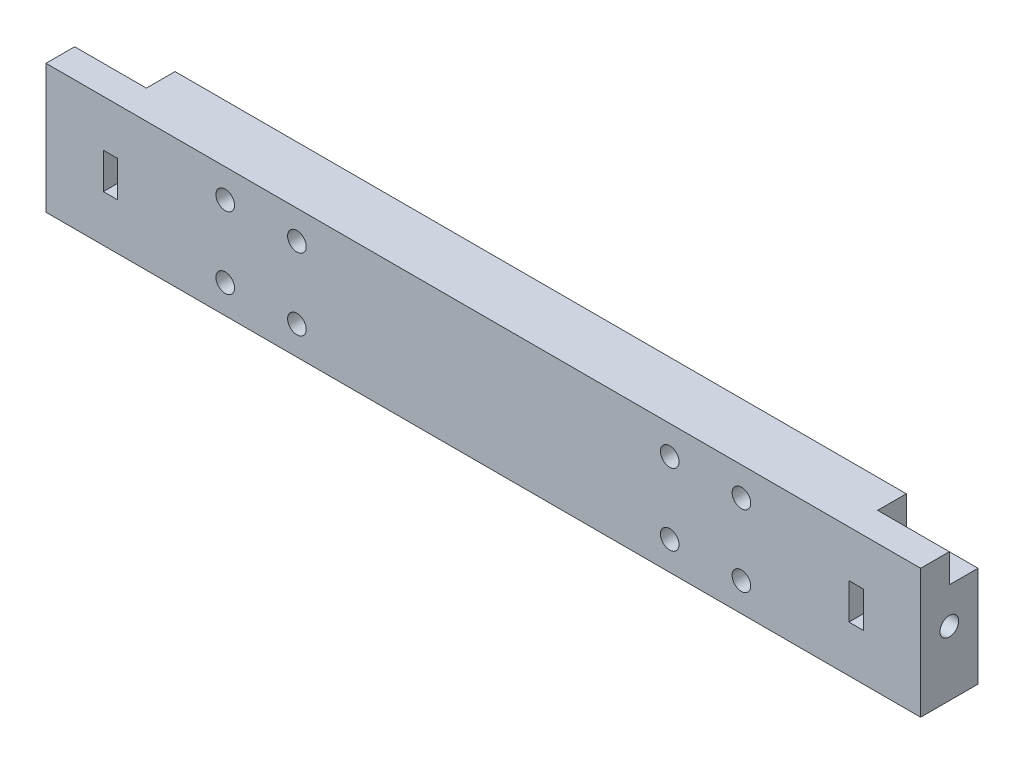
SolidWorks part; units mm, degrees
ref_plane "Front Plane" through (0, 0, 0) normal (0, 0, 1) x (1, 0, 0)
ref_plane "Top Plane" through (0, 0, 0) normal (0, 1, 0) x (1, 0, 0)
ref_plane "Right Plane" through (0, 0, 0) normal (1, 0, 0) x (0, 0, -1)
sketch "Sketch1" plane through (0, 0, 0) normal (0, 0, 1) x (1, 0, 0)
  line L1 (-61, 9) -> (61, 9)
  line L2 (-61, 9) -> (-61, -9)
  line L3 (-61, -9) -> (61, -9)
  line L4 (61, 9) -> (61, -9)
  line L5 (-61, 9) -> (61, -9) construction
  line L6 (-61, -9) -> (61, 9) construction
  line L7 (-36, 5) -> (36, 5) construction
  line L8 (-36, 5) -> (-36, -5) construction
  line L9 (-36, -5) -> (36, -5) construction
  line L10 (36, 5) -> (36, -5) construction
  line L11 (-36, 5) -> (36, -5) construction
  line L12 (-36, -5) -> (36, 5) construction
  line L13 (-26, 5) -> (26, 5) construction
  line L14 (-26, 5) -> (-26, -5) construction
  line L15 (-26, -5) -> (26, -5) construction
  line L16 (26, 5) -> (26, -5) construction
  line L17 (-26, 5) -> (26, -5) construction
  line L18 (-26, -5) -> (26, 5) construction
  circle A0 centre (-26, 5) radius 1.3
  circle A1 centre (-36, 5) radius 1.3
  circle A2 centre (-26, -5) radius 1.3
  circle A3 centre (-36, -5) radius 1.3
  circle A4 centre (26, -5) radius 1.3
  circle A5 centre (36, -5) radius 1.3
  circle A6 centre (36, 5) radius 1.3
  circle A7 centre (26, 5) radius 1.3
  point P0 (0, 0)
  point P6 (0, 0)
  point P11 (0, 0)
  dimension "D6" = 2.6
  dimension "D1" = 122
  dimension "D2" = 18
  dimension "D3" = 10
  dimension "D4" = 52
  dimension "D5" = 10
extrude "Boss-Extrude1" add sketch "Sketch1" along normal blind 8
sketch "Sketch2" plane through (0, 0, 0) normal (0, 0, -1) x (-1, 0, 0)
  line L1 (-36, 2) -> (-33.4019, 3.5)
  line L2 (-33.4019, 3.5) -> (-33.4019, 6.5)
  line L3 (-33.4019, 6.5) -> (-36, 8)
  line L4 (-36, 8) -> (-38.5981, 6.5)
  line L5 (-38.5981, 6.5) -> (-38.5981, 3.5)
  line L6 (-38.5981, 3.5) -> (-36, 2)
  line L7 (-26, 2) -> (-23.4019, 3.5)
  line L8 (-23.4019, 3.5) -> (-23.4019, 6.5)
  line L9 (-23.4019, 6.5) -> (-26, 8)
  line L10 (-26, 8) -> (-28.5981, 6.5)
  line L11 (-28.5981, 6.5) -> (-28.5981, 3.5)
  line L12 (-28.5981, 3.5) -> (-26, 2)
  line L13 (-26, -8) -> (-23.4019, -6.5)
  line L14 (-23.4019, -6.5) -> (-23.4019, -3.5)
  line L15 (-23.4019, -3.5) -> (-26, -2)
  line L16 (-26, -2) -> (-28.5981, -3.5)
  line L17 (-28.5981, -3.5) -> (-28.5981, -6.5)
  line L18 (-28.5981, -6.5) -> (-26, -8)
  line L19 (-36, -8) -> (-33.4019, -6.5)
  line L20 (-33.4019, -6.5) -> (-33.4019, -3.5)
  line L21 (-33.4019, -3.5) -> (-36, -2)
  line L22 (-36, -2) -> (-38.5981, -3.5)
  line L23 (-38.5981, -3.5) -> (-38.5981, -6.5)
  line L24 (-38.5981, -6.5) -> (-36, -8)
  line L25 (26, 2) -> (28.5981, 3.5)
  line L26 (28.5981, 3.5) -> (28.5981, 6.5)
  line L27 (28.5981, 6.5) -> (26, 8)
  line L28 (26, 8) -> (23.4019, 6.5)
  line L29 (23.4019, 6.5) -> (23.4019, 3.5)
  line L30 (23.4019, 3.5) -> (26, 2)
  line L31 (26, -8) -> (28.5981, -6.5)
  line L32 (28.5981, -6.5) -> (28.5981, -3.5)
  line L33 (28.5981, -3.5) -> (26, -2)
  line L34 (26, -2) -> (23.4019, -3.5)
  line L35 (23.4019, -3.5) -> (23.4019, -6.5)
  line L36 (23.4019, -6.5) -> (26, -8)
  line L37 (36, -8) -> (38.5981, -6.5)
  line L38 (38.5981, -6.5) -> (38.5981, -3.5)
  line L39 (38.5981, -3.5) -> (36, -2)
  line L40 (36, -2) -> (33.4019, -3.5)
  line L41 (33.4019, -3.5) -> (33.4019, -6.5)
  line L42 (33.4019, -6.5) -> (36, -8)
  line L43 (36, 2) -> (38.5981, 3.5)
  line L44 (38.5981, 3.5) -> (38.5981, 6.5)
  line L45 (38.5981, 6.5) -> (36, 8)
  line L46 (36, 8) -> (33.4019, 6.5)
  line L47 (33.4019, 6.5) -> (33.4019, 3.5)
  line L48 (33.4019, 3.5) -> (36, 2)
  circle A0 centre (-36, 5) radius 2.5981 construction
  circle A1 centre (-26, 5) radius 2.5981 construction
  circle A2 centre (-26, -5) radius 2.5981 construction
  circle A3 centre (-36, -5) radius 2.5981 construction
  circle A4 centre (26, 5) radius 2.5981 construction
  circle A5 centre (26, -5) radius 2.5981 construction
  circle A6 centre (36, -5) radius 2.5981 construction
  circle A7 centre (36, 5) radius 2.5981 construction
  dimension "D1" = 6
extrude "Cut-Extrude1" cut sketch "Sketch2" against normal blind 3
sketch "Sketch3" plane through (0, 0, 0) normal (0, 0, -1) x (-1, 0, 0)
  line L1 (-61, 9) -> (-51, 9)
  line L2 (-61, 9) -> (-61, 5)
  line L3 (-61, 5) -> (-51, 5)
  line L4 (-51, 9) -> (-51, 5)
  line L5 (61, 9) -> (51, 9)
  line L6 (61, 9) -> (61, 5)
  line L7 (61, 5) -> (51, 5)
  line L8 (51, 9) -> (51, 5)
  dimension "D1" = 10
  dimension "D2" = 4
extrude "Cut-Extrude2" cut sketch "Sketch3" against normal blind 4
sketch "Sketch4" plane through (61, 0, 0) normal (1, 0, 0) x (0, 0, -1)
  line L0 (-4, 5) -> (-4, 0) construction
  line L1 (-4, 0) -> (0, 0) construction
  circle A0 centre (-4, 0) radius 1.3
  dimension "D1" = 2.6
extrude "Cut-Extrude3" cut sketch "Sketch4" against normal blind 10
sketch "Sketch5" plane through (0, 0, 0) normal (0, 0, -1) x (-1, 0, 0)
  line L0 (-61, 0) -> (61, 0) construction
  line L1 (-51, 2.5) -> (-53, 2.5)
  line L2 (-51, 2.5) -> (-51, -2.5)
  line L3 (-51, -2.5) -> (-53, -2.5)
  line L4 (-53, 2.5) -> (-53, -2.5)
  line L5 (-61, -9) -> (-61, 5) construction
  line L6 (61, 5) -> (61, -9) construction
  line L7 (-51, 5) -> (-51, 9) construction
  point P13 (-53, 0)
  dimension "D1" = 2
  dimension "D2" = 5
extrude "Cut-Extrude4" cut sketch "Sketch5" against normal blind 10
mirror "Mirror1" about plane through (0, 0, 0) normal (1, 0, 0) of "Cut-Extrude4", "Cut-Extrude3"
